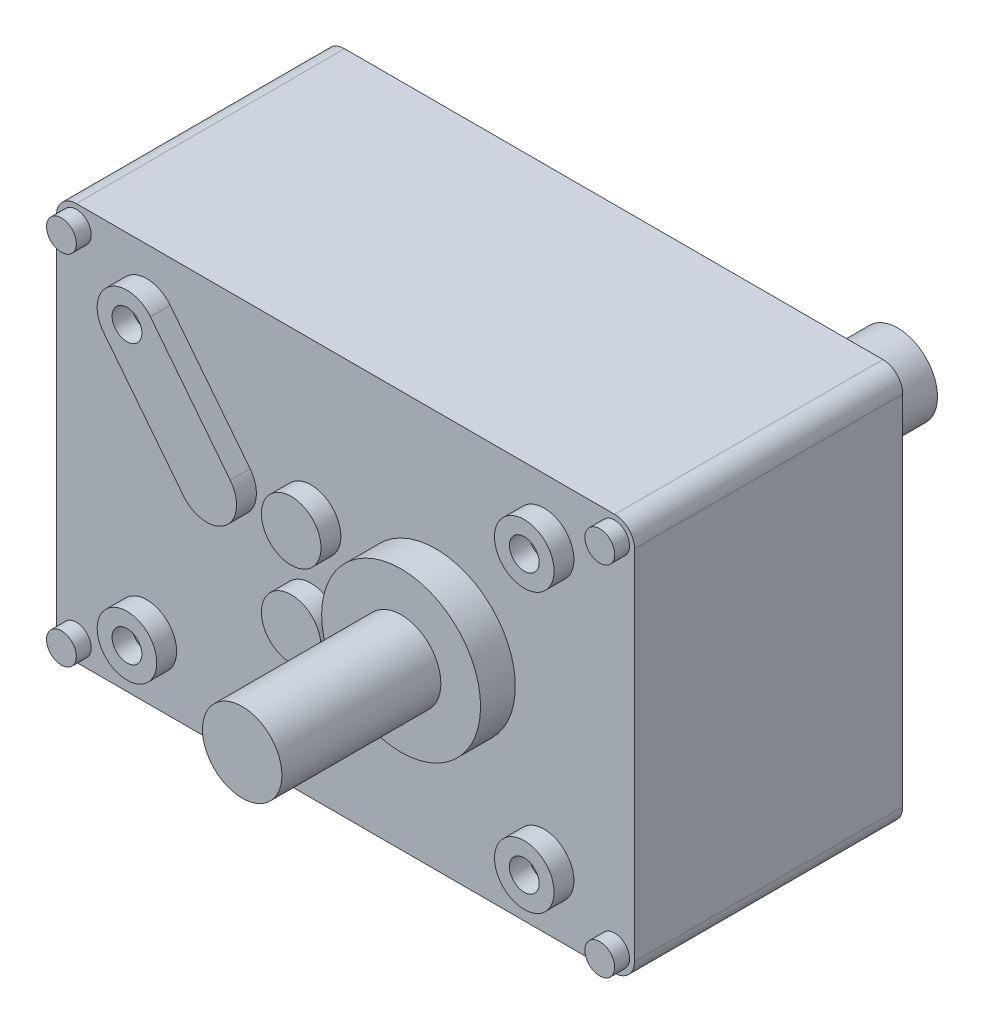
SolidWorks part; units mm, degrees
ref_plane "前视基准面" through (0, 0, 0) normal (0, 0, 1) x (1, 0, 0)
ref_plane "上视基准面" through (0, 0, 0) normal (0, 1, 0) x (1, 0, 0)
ref_plane "右视基准面" through (0, 0, 0) normal (1, 0, 0) x (0, 0, -1)
sketch "草图1" plane through (0, 0, 0) normal (0, 0, 1) x (1, 0, 0)
  line L1 (-29.1, -20) -> (29.1, -20)
  line L2 (-29.1, -20) -> (-29.1, 20)
  line L3 (-29.1, 20) -> (29.1, 20)
  line L4 (29.1, -20) -> (29.1, 20)
  line L5 (-29.1, -20) -> (29.1, 20) construction
  line L6 (-29.1, 20) -> (29.1, -20) construction
  point P0 (0, 0)
  dimension "D1" = 58.2
  dimension "D2" = 40
extrude "凸台-拉伸1" add sketch "草图1" against normal blind 13.5
sketch "草图2" plane through (0, 0, 0) normal (0, 0, 1) x (1, 0, 0)
  line L0 (29.1, 0) -> (9.1, 0) construction
  line L2 (29.1, -20) -> (29.1, 20) construction
  line L3 (9.1, 0) -> (9.1, 21.7297) construction
  line L4 (9.1, 21.7297) -> (9.1, -26.0935) construction
  circle A0 centre (9.1, 0) radius 8
  dimension "D1" = 16
extrude "凸台-拉伸2" add sketch "草图2" along normal blind 3.5
sketch "草图3" plane through (0, 0, 0) normal (0, 0, 1) x (1, 0, 0)
sketch "草图4" plane through (0, 0, 0) normal (0, 0, 1) x (1, 0, 0)
  circle A0 centre (9.1, 0) radius 4
  dimension "D1" = 8
extrude "凸台-拉伸3" add sketch "草图4" along normal blind 19.5
sketch "草图5" plane through (0, 0, 0) normal (0, 0, 1) x (1, 0, 0)
  line L0 (29.1, 0) -> (9.1, 0) construction
  line L1 (9.1, 0) -> (9.1, 21.7297) construction
  line L2 (0, 0) -> (0, -4.2139)
  line L3 (0, 0) -> (-3.2672, 0)
  line L4 (-20, 14) -> (-11.9679, 3.7782) construction
  line L5 (-17.6411, 15.8536) -> (-9.609, 5.6318)
  line L6 (-22.3589, 12.1464) -> (-14.3267, 1.9246)
  circle A1 centre (20, 14) radius 1.5
  circle A2 centre (-20, 14) radius 1.5
  circle A5 centre (20, 14) radius 3
  circle A6 centre (20, -14) radius 1.5
  circle A7 centre (20, -14) radius 3
  arc A10 (-17.6411, 15.8536) -> (-22.3589, 12.1464) centre (-20, 14) ccw
  arc A11 (-14.3267, 1.9246) -> (-9.609, 5.6318) centre (-11.9679, 3.7782) ccw
  circle A12 centre (-3.4679, 4.2853) radius 3
  circle A13 centre (-20, -14) radius 1.5
  circle A14 centre (-20, -14) radius 3
  circle A15 centre (-3.4679, -4.2853) radius 3
  point P19 (-15.9839, 8.8891)
  dimension "D1" = 3
  dimension "D4" = 6
  dimension "D5" = 3
  dimension "D7" = 6
  dimension "D8" = 3
  dimension "D2" = 14
  dimension "D3" = 10.9
  dimension "D6" = 13
  dimension "D9" = 21.0679
  dimension "D10" = 8.5
extrude "凸台-拉伸4" add sketch "草图5" along normal blind 2
mirror "镜向2" about plane through (0, 0, -13.5) normal (0, 0, -1) of "凸台-拉伸2", "凸台-拉伸3", "凸台-拉伸4", "凸台-拉伸1"
sketch "草图6" plane through (0, 0, 0) normal (0, 0, 1) x (1, 0, 0)
  line L0 (0, 0) -> (0, 7.7617)
  line L1 (0, 0) -> (-4.0248, 0)
  line L2 (29.1, 20) -> (-29.1, 20) construction
  line L3 (29.1, -20) -> (29.1, 20) construction
  circle A0 centre (27.1, 18) radius 1.5
  circle A1 centre (-27.1, 18) radius 1.5
  circle A2 centre (27.1, -18) radius 1.5
  circle A3 centre (-27.1, -18) radius 1.5
  dimension "D1" = 3
  dimension "D2" = 2
  dimension "D3" = 2
extrude "凸台-拉伸5" add sketch "草图6" along normal blind 1.5 contours A1 | A3 | A2 | A0
fillet "圆角1" radius 2 4 edges at (-29.1, -20, -13.5) (29.1, -20, -13.5) (-29.1, 20, -13.5) (29.1, 20, -13.5)
sketch "草图7" plane through (-29.1, 0, 0) normal (-1, 0, 0) x (0, 0, 1)
  circle A0 centre (-11.5, 2) radius 6.5
  dimension "D1" = 13
extrude "切除-拉伸1" cut sketch "草图7" against normal blind 15
ref_plane "基准面1" through (0, 0, -13.5) normal (0, 0, 1) x (1, 0, 0)
